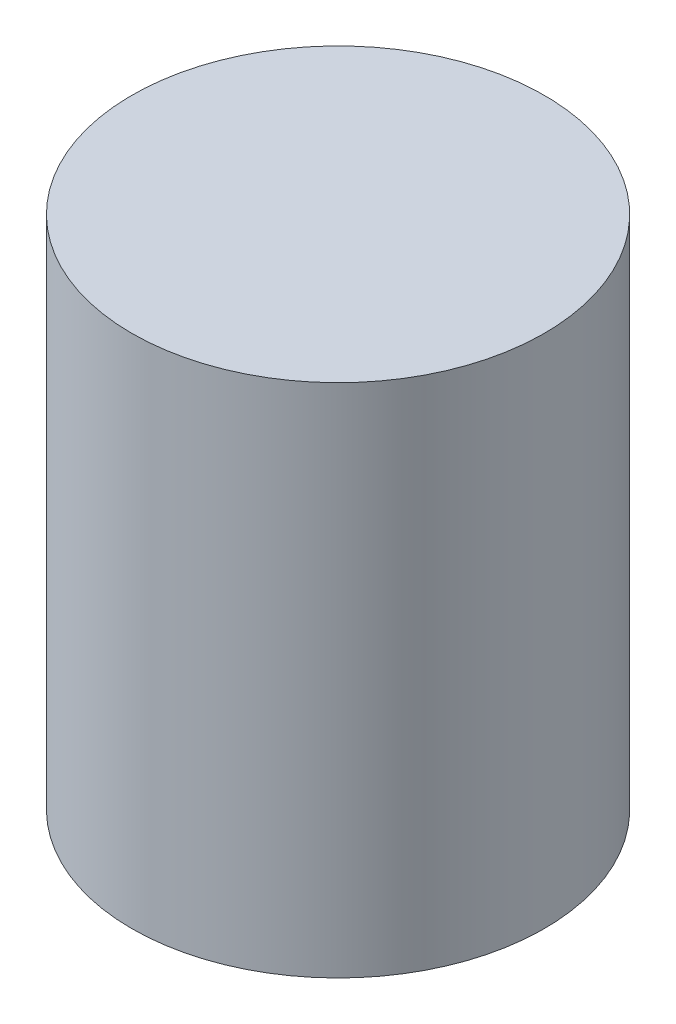
SolidWorks part; units mm, degrees
ref_plane "Front Plane" through (0, 0, 0) normal (0, 0, 1) x (1, 0, 0)
ref_plane "Top Plane" through (0, 0, 0) normal (0, 1, 0) x (1, 0, 0)
ref_plane "Right Plane" through (0, 0, 0) normal (1, 0, 0) x (0, 0, -1)
sketch "Sketch1" plane through (0, 0, 0) normal (0, 1, 0) x (1, 0, 0)
  circle A0 centre (0, 0) radius 2
  dimension "D1" = 4
extrude "Boss-Extrude1" add sketch "Sketch1" along normal blind 5 contours A0
